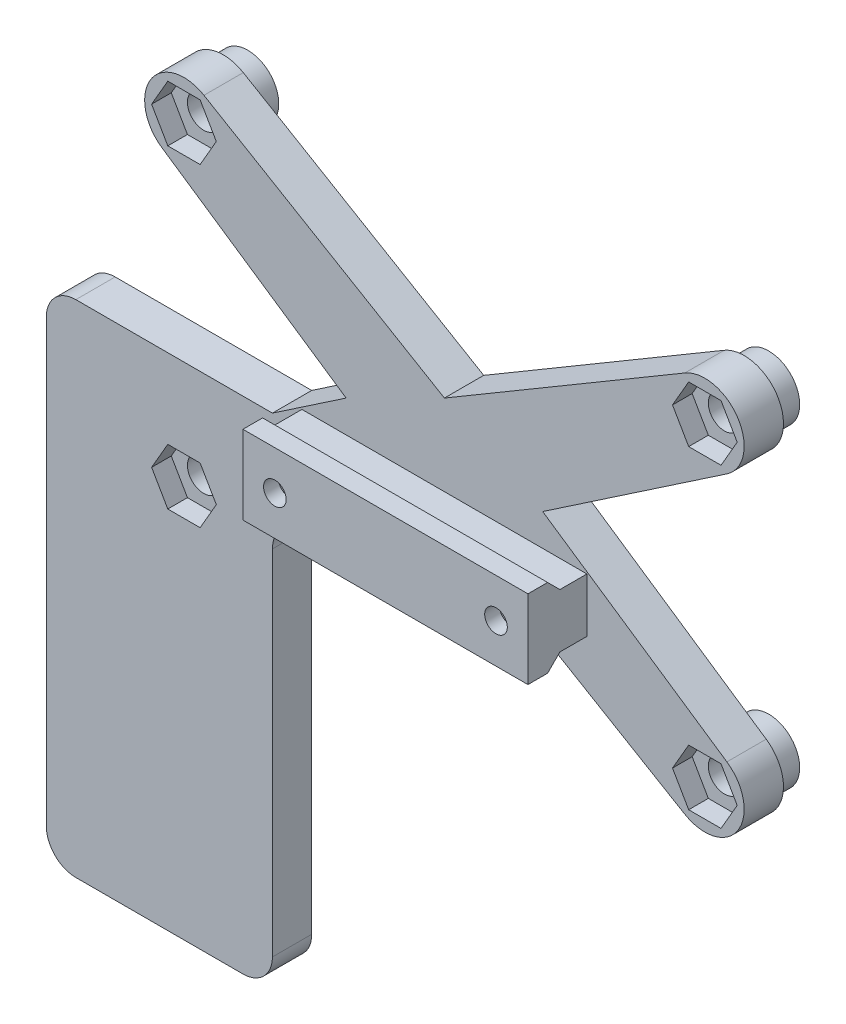
SolidWorks part; units mm, degrees
ref_plane "前视基准面" through (0, 0, 0) normal (0, 0, 1) x (1, 0, 0)
ref_plane "上视基准面" through (0, 0, 0) normal (0, 1, 0) x (1, 0, 0)
ref_plane "右视基准面" through (0, 0, 0) normal (1, 0, 0) x (0, 0, -1)
sketch "草图1" plane through (0, 0, 0) normal (0, 0, 1) x (1, 0, 0)
  line L0 (30.5, 20) -> (-30.5, -20) construction
  line L1 (30.5, 20) -> (-30.5, 20) construction
  line L2 (30.5, 20) -> (30.5, -20) construction
  line L3 (30.5, -20) -> (-30.5, -20) construction
  line L4 (-30.5, 20) -> (-30.5, -20) construction
  line L5 (-24.4664, 19.4445) -> (0, 5)
  line L6 (-26.5, 16) -> (26.5, 16) construction
  line L7 (-26.5, 16) -> (-26.5, -16) construction
  line L8 (-26.5, -16) -> (26.5, -16) construction
  line L9 (26.5, 16) -> (26.5, -16) construction
  line L10 (-26.5, 16) -> (26.5, -16) construction
  line L11 (-26.5, -16) -> (26.5, 16) construction
  line L12 (-24.4664, -19.4445) -> (0, -5)
  line L13 (0, 5) -> (0, -5) construction
  line L14 (24.4664, -19.4445) -> (0, -5)
  line L15 (-28.7423, 12.6876) -> (-10, 0)
  line L16 (-10, 0) -> (-28.7423, -12.6876)
  line L17 (10, 0) -> (28.7423, -12.6876)
  line L18 (28.7423, 12.6876) -> (10, 0)
  line L19 (24.4664, 19.4445) -> (0, 5)
  arc A0 (-24.4664, 19.4445) -> (-28.7423, 12.6876) centre (-26.5, 16) ccw
  arc A3 (-28.7423, -12.6876) -> (-24.4664, -19.4445) centre (-26.5, -16) ccw
  arc A4 (28.7423, -12.6876) -> (24.4664, -19.4445) centre (26.5, -16) cw
  arc A5 (24.4664, 19.4445) -> (28.7423, 12.6876) centre (26.5, 16) cw
  circle A6 centre (-26.5, 16) radius 1.65
  circle A7 centre (26.5, 16) radius 1.65
  circle A8 centre (26.5, -16) radius 1.65
  circle A9 centre (-26.5, -16) radius 1.65
  point P4 (0, 0)
  point P9 (0, 0)
  point P10 (0, 0)
  dimension "D5" = 8
  dimension "D8" = 3.3
  dimension "D1" = 40
  dimension "D2" = 61
  dimension "D3" = 32
  dimension "D4" = 53
  dimension "D6" = 10
  dimension "D7" = 10
extrude "凸台-拉伸1" add sketch "草图1" along normal blind 4
sketch "草图2" plane through (0, 0, 4) normal (0, 0, 1) x (1, 0, 0)
  line L1 (-24.8546, 18.85) -> (-28.1454, 18.85)
  line L2 (-28.1454, 18.85) -> (-29.7909, 16)
  line L3 (-29.7909, 16) -> (-28.1454, 13.15)
  line L4 (-28.1454, 13.15) -> (-24.8546, 13.15)
  line L5 (-24.8546, 13.15) -> (-23.2091, 16)
  line L6 (-23.2091, 16) -> (-24.8546, 18.85)
  line L7 (28.1454, 18.85) -> (24.8546, 18.85)
  line L8 (24.8546, 18.85) -> (23.2091, 16)
  line L9 (23.2091, 16) -> (24.8546, 13.15)
  line L10 (24.8546, 13.15) -> (28.1454, 13.15)
  line L11 (28.1454, 13.15) -> (29.7909, 16)
  line L12 (29.7909, 16) -> (28.1454, 18.85)
  line L13 (28.1454, -13.15) -> (24.8546, -13.15)
  line L14 (24.8546, -13.15) -> (23.2091, -16)
  line L15 (23.2091, -16) -> (24.8546, -18.85)
  line L16 (24.8546, -18.85) -> (28.1454, -18.85)
  line L17 (28.1454, -18.85) -> (29.7909, -16)
  line L18 (29.7909, -16) -> (28.1454, -13.15)
  line L19 (-24.8546, -13.15) -> (-28.1454, -13.15)
  line L20 (-28.1454, -13.15) -> (-29.7909, -16)
  line L21 (-29.7909, -16) -> (-28.1454, -18.85)
  line L22 (-28.1454, -18.85) -> (-24.8546, -18.85)
  line L23 (-24.8546, -18.85) -> (-23.2091, -16)
  line L24 (-23.2091, -16) -> (-24.8546, -13.15)
  circle A0 centre (-26.5, 16) radius 2.85 construction
  circle A1 centre (26.5, 16) radius 2.85 construction
  circle A2 centre (26.5, -16) radius 2.85 construction
  circle A3 centre (-26.5, -16) radius 2.85 construction
  dimension "D1" = 5.7
extrude "切除-拉伸1" cut sketch "草图2" against normal offset from surface (2 mm away) 2 up to face at (-24.85, 16, 0)
sketch "草图5" plane through (0, 0, 0) normal (0, 0, -1) x (-1, 0, 0)
  circle A0 centre (26.5, 16) radius 1.65 construction
  circle A1 centre (26.5, -16) radius 1.65 construction
  circle A2 centre (-26.5, -16) radius 1.65 construction
  circle A3 centre (-26.5, 16) radius 1.65 construction
  circle A4 centre (26.5, 16) radius 1.65
  circle A5 centre (26.5, -16) radius 1.65
  circle A6 centre (-26.5, -16) radius 1.65
  circle A7 centre (-26.5, 16) radius 1.65
  circle A8 centre (26.5, 16) radius 3.15
  circle A9 centre (26.5, -16) radius 3.15
  circle A10 centre (-26.5, -16) radius 3.15
  circle A11 centre (-26.5, 16) radius 3.15
  dimension "D1" = 1.5
extrude "凸台-拉伸3" add sketch "草图5" along normal blind 2.5
sketch "草图3" plane through (0, 0, 0) normal (1, 0, 0) x (0, 0, -1)
  line L0 (0, -8.75) -> (0, -3.25)
  line L1 (0, -12.6876) -> (0, 0) construction
  line L3 (-10, -2) -> (-10, -10)
  line L4 (-10, -10) -> (-8, -10)
  line L5 (-8, -10) -> (-6.75, -8.75)
  line L6 (0, -8.75) -> (-6.75, -8.75)
  line L9 (-6.75, -3.25) -> (0, -3.25)
  line L10 (-10, -2) -> (-8, -2)
  line L11 (-8, -2) -> (-6.75, -3.25)
  line L12 (2.5, -19.15) -> (2.5, -12.85) construction
  line L13 (2.5, -19.15) -> (2.5, -12.85) construction
  point P12 (0, -6)
  point P14 (2.5, -16)
  dimension "D1" = 135
  dimension "D2" = 8
  dimension "D3" = 5.5
  dimension "D4" = 135
  dimension "D5" = 2
  dimension "D6" = 10
  dimension "D7" = 10
extrude "凸台-拉伸2" add sketch "草图3" along normal mid plane 29
sketch "草图4" plane through (0, 0, 10) normal (0, 0, 1) x (1, 0, 0)
  line L0 (-11.25, -6) -> (11.25, -6) construction
  line L2 (14.5, -3.25) -> (14.5, -8.75) construction
  circle A0 centre (-11.25, -6) radius 1.15
  circle A1 centre (11.25, -6) radius 1.15
  point P5 (0, -6)
  point P9 (14.5, -6)
  dimension "D2" = 2.3
  dimension "D1" = 22.5
extrude "切除-拉伸2" cut sketch "草图4" against normal through all
sketch "草图6" plane through (0, 0, 0) normal (0, 0, -1) x (-1, 0, 0)
  line L1 (-10.0664, -3.95) -> (-12.4336, -3.95)
  line L2 (-12.4336, -3.95) -> (-13.6171, -6)
  line L3 (-13.6171, -6) -> (-12.4336, -8.05)
  line L4 (-12.4336, -8.05) -> (-10.0664, -8.05)
  line L5 (-10.0664, -8.05) -> (-8.8829, -6)
  line L6 (-8.8829, -6) -> (-10.0664, -3.95)
  line L7 (12.4336, -3.95) -> (10.0664, -3.95)
  line L8 (10.0664, -3.95) -> (8.8829, -6)
  line L9 (8.8829, -6) -> (10.0664, -8.05)
  line L10 (10.0664, -8.05) -> (12.4336, -8.05)
  line L11 (12.4336, -8.05) -> (13.6171, -6)
  line L12 (13.6171, -6) -> (12.4336, -3.95)
  circle A0 centre (-11.25, -6) radius 2.05 construction
  circle A1 centre (11.25, -6) radius 2.05 construction
  dimension "D1" = 4.1
extrude "切除-拉伸3" cut sketch "草图6" against normal offset from surface (8.5 mm away) 1.5 up to face at (-10.1, -6, 10)
sketch "草图7" plane through (0, 0, 0) normal (0, 0, -1) x (-1, 0, 0)
  line L0 (10, 0) -> (28.7423, -12.6876) construction
  line L1 (17.5, -5.0771) -> (40.5, -5.0771)
  line L2 (17.5, -15.3317) -> (17.5, -56)
  line L3 (17.5, -56) -> (40.5, -56)
  line L4 (40.5, -5.0771) -> (40.5, -56)
  line L5 (24.4664, -19.4445) -> (6.3518, -8.75) construction
  line L6 (24.4664, -19.4445) -> (17.5, -15.3317)
  line L7 (17.5, -5.0771) -> (28.7423, -12.6876)
  circle A0 centre (26.5, -16) radius 1.65 construction
  arc A1 (24.4664, -19.4445) -> (28.7423, -12.6876) centre (26.5, -16) ccw construction
  arc A2 (24.4664, -19.4445) -> (28.7423, -12.6876) centre (26.5, -16) ccw
  dimension "D1" = 23
  dimension "D2" = 17.5
  dimension "D3" = 40
extrude "凸台-拉伸4" add sketch "草图7" against normal up to surface (4 mm away) up to face at (-26.5, 16, 4)
fillet "圆角1" radius 3 4 edges at (-17.5, -56, 2) (-40.5, -56, 2) (-40.5, -5.0771, 2) (-17.5, -15.3317, 2)
